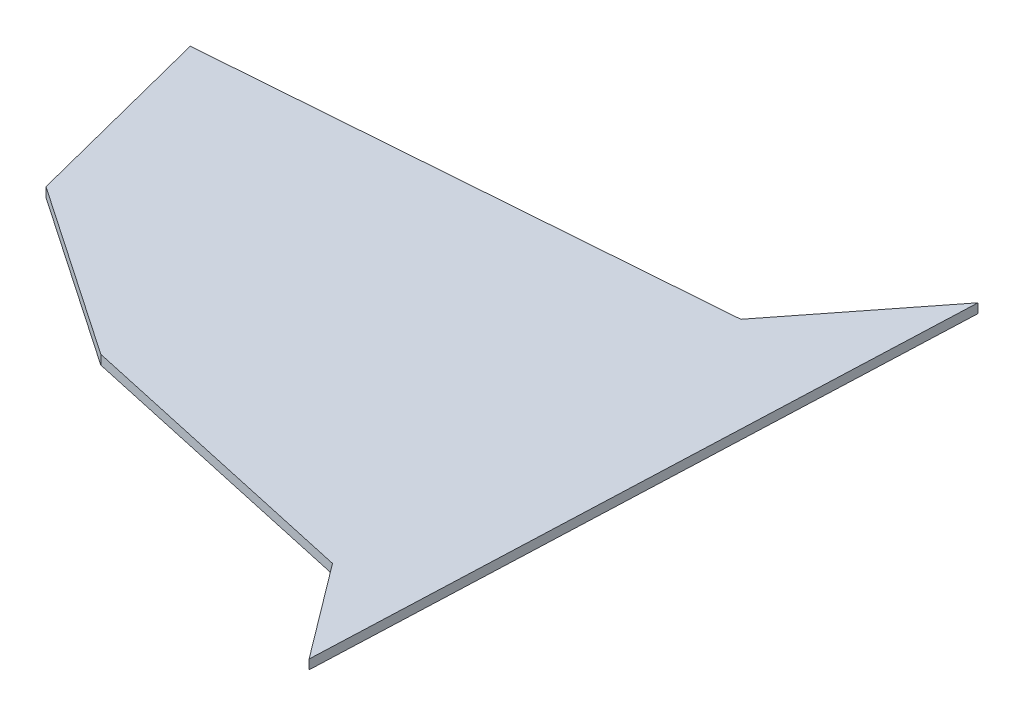
SolidWorks part; units mm, degrees
ref_plane "Plan de face" through (0, 0, 0) normal (0, 0, 1) x (1, 0, 0)
ref_plane "Plan de dessus" through (0, 0, 0) normal (0, 1, 0) x (1, 0, 0)
ref_plane "Plan de droite" through (0, 0, 0) normal (1, 0, 0) x (0, 0, -1)
sketch "Esquisse2" plane through (0, 0, 0) normal (0, 1, 0) x (1, 0, 0)
  line L0 (120.7374, 77.8903) -> (98.5112, 49.5726)
  line L1 (98.5112, 49.5726) -> (-10.5667, 41.3077)
  line L2 (-10.5667, 41.3077) -> (0, 0)
  line L3 (0, 0) -> (36.7642, -25.0875)
  line L4 (36.7642, -25.0875) -> (100.0617, -38.9977)
  line L5 (100.0617, -38.9977) -> (115.2047, -59.1334)
  line L6 (115.2047, -59.1334) -> (120.7374, 77.8903)
  point P7 (0, 0)
extrude "Boss.-Extru.1" add sketch "Esquisse2" along normal blind 2
